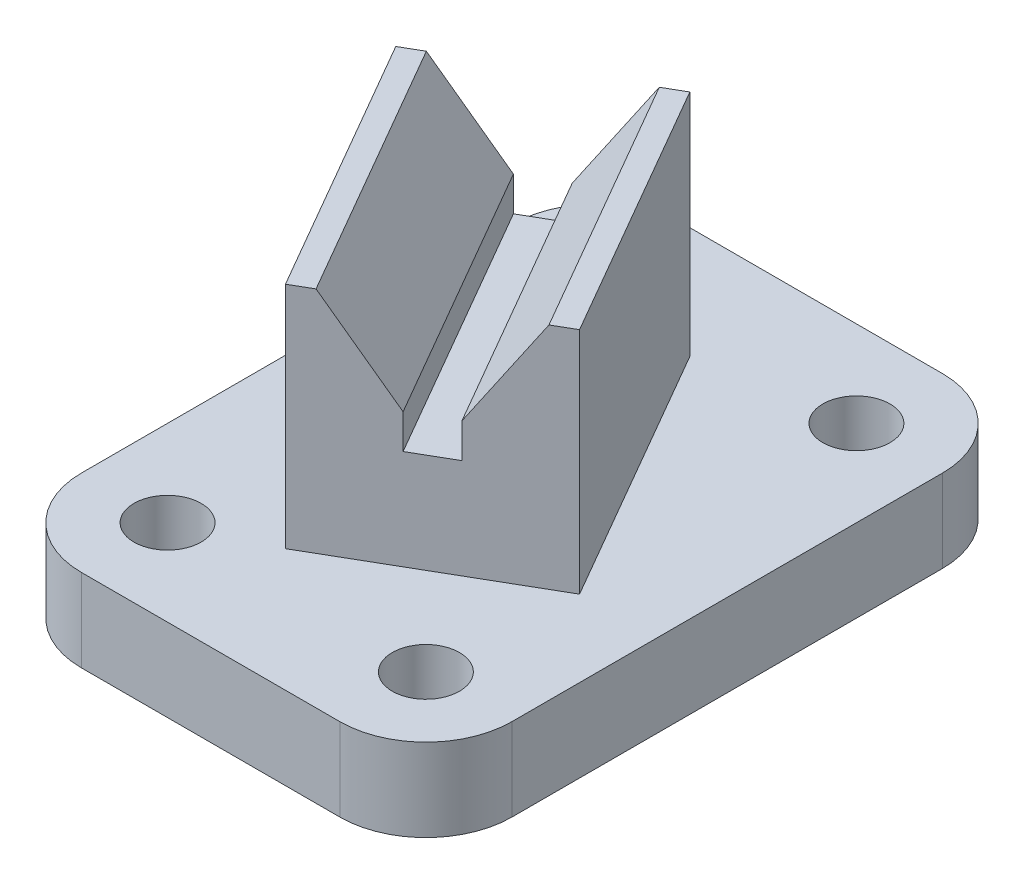
SolidWorks part; units mm, degrees
ref_plane "Frontal" through (0, 0, 0) normal (0, 0, 1) x (1, 0, 0)
ref_plane "Horizontal" through (0, 0, 0) normal (0, 1, 0) x (1, 0, 0)
ref_plane "Profile" through (0, 0, 0) normal (1, 0, 0) x (0, 0, -1)
sketch "Sketch1" plane through (0, 0, 0) normal (0, 1, 0) x (1, 0, 0)
  line L1 (-29.6649, 41.7726) -> (33.8351, 41.7726)
  line L2 (-29.6649, 41.7726) -> (-29.6649, -47.1274)
  line L3 (-29.6649, -47.1274) -> (33.8351, -47.1274)
  line L4 (33.8351, 41.7726) -> (33.8351, -47.1274)
  dimension "D1" = 88.9
  dimension "D2" = 63.5
extrude "Extrude1" add sketch "Sketch1" against normal blind 12.192
sketch "Sketch2" plane through (0, 0, 0) normal (0, 1, 0) x (-1, 0, 0)
  line L0 (29.6649, 47.1274) -> (-33.8351, 47.1274) construction
  line L1 (-33.8351, 47.1274) -> (-33.8351, -41.7726) construction
  circle A0 centre (-21.1351, 34.4274) radius 4.953
  dimension "D1" = 12.7
  dimension "D2" = 12.7
extrude "Cut-Extrude1" cut sketch "Sketch2" against normal through all
sketch "Sketch3" plane through (0, 0, 0) normal (0, 1, 0) x (-1, 0, 0)
  line L0 (-21.1351, 34.4274) -> (-21.1351, -30.1256) construction
  line L1 (-21.1351, 34.4274) -> (22.9779, 34.4274) construction
pattern_linear "LPattern1" count 2 spacing 63.5 along (0, 0, -1) count 2 spacing 38.1 along (-1, 0, 0) of "Cut-Extrude1"
fillet "Fillet1" radius 12.7 4 edges at (-29.6649, -6.096, -41.7726) (33.8351, -6.096, -41.7726) (33.8351, -6.096, 47.1274) (-29.6649, -6.096, 47.1274)
sketch "Sketch4" plane through (0, 0, 0) normal (0, 1, 0) x (-1, 0, 0)
  line L0 (-0.3133, -25.3251) -> (-22.5383, 13.1698)
  line L1 (-22.5383, 13.1698) -> (4.958, 29.0448)
  line L4 (-0.3133, -25.3251) -> (27.183, -9.4501)
  line L5 (27.183, -9.4501) -> (4.958, 29.0448)
  dimension "D1" = 31.75
  dimension "D2" = 44.45
extrude "Extrude2" add sketch "Sketch4" along normal blind 33.782
sketch "Sketch5" plane through (11.3373, 0, 19.6367) normal (0.5, 0, 0.866) x (0.866, 0, -0.5)
  line L0 (-15.5141, 33.782) -> (-6.1161, 19.812)
  line L1 (-18.8161, 33.782) -> (12.9339, 33.782) construction
  line L2 (-6.1161, 19.812) -> (-6.1161, 14.732)
  line L3 (-6.1161, 14.732) -> (0.2339, 14.732)
  line L4 (0.2339, 14.732) -> (0.2339, 19.812)
  line L5 (0.2339, 19.812) -> (9.6319, 33.782)
  line L6 (-2.9411, 0) -> (-2.9411, 33.782) construction
  line L7 (-18.8161, 0) -> (12.9339, 0) construction
  point P12 (-2.9411, 14.732)
  dimension "D1" = 6.35
  dimension "D2" = 3.302
  dimension "D3" = 3.302
  dimension "D4" = 19.05
  dimension "D5" = 5.08
extrude "Cut-Extrude3" cut sketch "Sketch5" against normal through all
